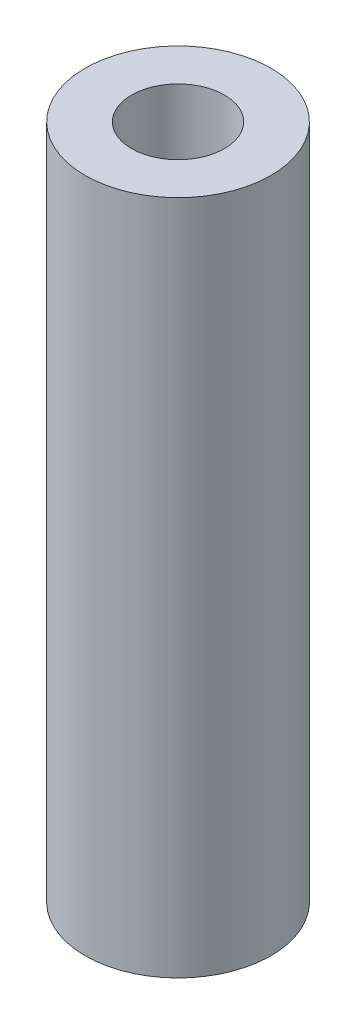
SolidWorks part; units mm, degrees
ref_plane "Front Plane" through (0, 0, 0) normal (0, 0, 1) x (1, 0, 0)
ref_plane "Top Plane" through (0, 0, 0) normal (0, 1, 0) x (1, 0, 0)
ref_plane "Right Plane" through (0, 0, 0) normal (1, 0, 0) x (0, 0, -1)
sketch "Sketch1" plane through (0, 0, 0) normal (0, 1, 0) x (1, 0, 0)
  circle A0 centre (0, 0) radius 5.5
  circle A1 centre (0, 0) radius 11
  dimension "D1" = 22
  dimension "D2" = 11
extrude "Boss-Extrude1" add sketch "Sketch1" along normal mid plane 80
